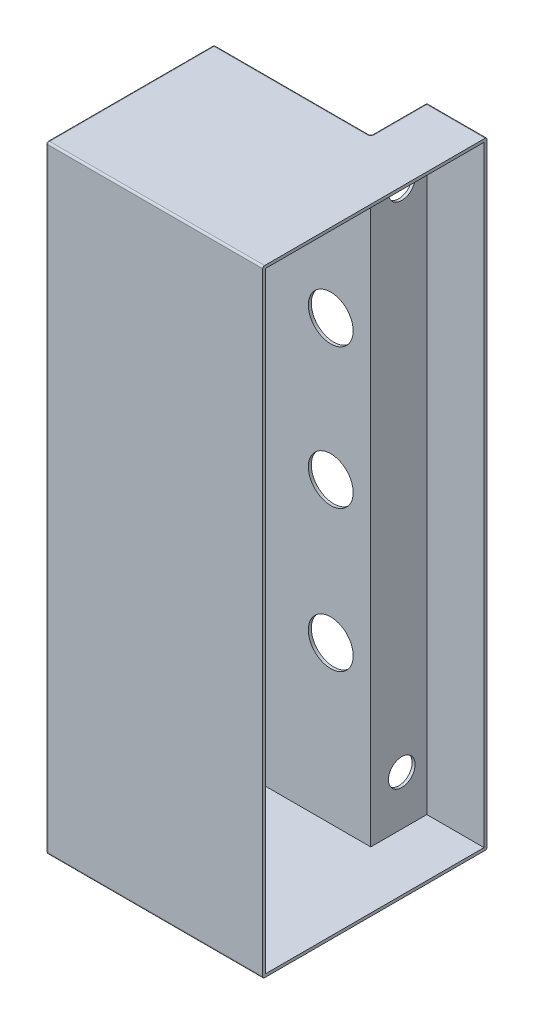
SolidWorks part; units mm, degrees
other "标注1"
sketch "草图10" plane through (-55, 0, -5) normal (-1, 0, 0) x (0, 0, 1)
ref_plane "前视基准面" through (0, 0, 0) normal (0, 0, 1) x (1, 0, 0)
ref_plane "上视基准面" through (0, 0, 0) normal (0, 1, 0) x (1, 0, 0)
ref_plane "右视基准面" through (0, 0, 0) normal (1, 0, 0) x (0, 0, -1)
other "Configuration Table"
sketch "草图1" plane through (0, 0, 0) normal (0, 1, 0) x (1, 0, 0)
  line L0 (3, 5) -> (3, -55)
  line L1 (3, -55) -> (-55, -55)
  line L2 (-55, -55) -> (-55, -10)
  line L3 (-55, -10) -> (-13.1, -10)
  line L4 (-13.1, -10) -> (-13.1, 5)
  line L5 (-13.1, 5) -> (3, 5)
  point P6 (0, 0)
  point P7 (0, 0)
  point P8 (0, 0)
extrude "凸台-拉伸1" add sketch "草图1" along normal blind 165
sketch "草图2" plane through (0, 0, 10) normal (0, 0, -1) x (-1, 0, 0)
  circle A0 centre (23, 42.75) radius 6
  circle A1 centre (23, 118) radius 6
  circle A2 centre (23, 80.55) radius 6
shell "抽壳1" thickness 0.8
extrude "切除-拉伸4" cut sketch "草图2" against normal blind 1 contours A0 | A2 | A1
fillet "圆角1" radius 0.5 14 edges at (-5.05, 0, -5) (-13.1, 0, 2.5) (-13.1, 82.5, 10) (-13.1, 82.5, -5) (-26, 0, 55) (-34.05, 0, 10) (-55, 0, 32.5) (-55, 82.5, 10) (-5.05, 165, -5) (-13.1, 165, 2.5) (-34.05, 165, 10) (-55, 165, 32.5) (-26, 165, 55) (-55, 82.5, 55)
sketch "草图8" plane through (-13.1, 0, 0) normal (-1, 0, 0) x (0, 0, 1)
  point P0 (2.5, 150)
  point P1 (2.5, 14)
hole_wizard "9/32 (0.28125) 直径孔1" positions "草图8" profile "草图9" hole size "9/32" standard "ANSI Inch" end condition through all
sketch "草图9" plane through (-13.1, 150, 2.5) normal (0, 1, 0) x (0, 0, 1)
  line L0 (0, 0) -> (0, 16.1)
  line L1 (0, 16.1) -> (3.5719, 16.1)
  line L2 (3.5719, 16.1) -> (3.5719, 0)
  line L5 (3.5719, 0) -> (0, 0)
  line L11 (0, -6.35) -> (0, 107.95) construction
  dimension "通孔孔直径" = 7.1437
  dimension "通孔孔深度" = 16.1
sketch "草图11" plane through (-55, 0, 0) normal (-1, 0, 0) x (0, 0, 1)
  text T0 "<r90><b><i>OCCUPIED</i></b>" font "汉仪长仿宋体" height 3.5
  text T1 "<b><r90><i>AWAY</i></b>" font "汉仪长仿宋体" height 3.5
  text T2 "<b><i><r90>OPEN</i></b>" font "汉仪长仿宋体" height 3.5
